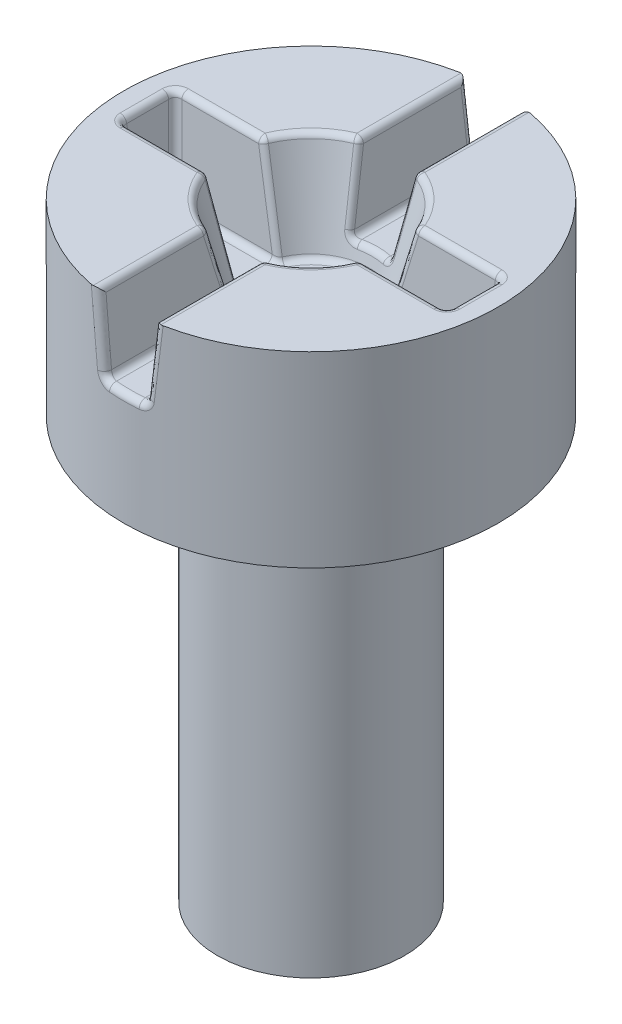
SolidWorks part; units mm, degrees
ref_plane "Front Plane" through (0, 0, 0) normal (0, 0, 1) x (1, 0, 0)
ref_plane "Top Plane" through (0, 0, 0) normal (0, 1, 0) x (1, 0, 0)
ref_plane "Right Plane" through (0, 0, 0) normal (1, 0, 0) x (0, 0, -1)
sketch "Sketch1" plane through (0, 0, 0) normal (0, 1, 0) x (1, 0, 0)
  circle A0 centre (0, 0) radius 1
  dimension "D1" = 2
extrude "Boss-Extrude1" add sketch "Sketch1" against normal blind 4.5
sketch "Sketch2" plane through (0, 0, 0) normal (0, 1, 0) x (1, 0, 0)
  circle A0 centre (0, 0) radius 2
  dimension "D1" = 4
extrude "Boss-Extrude2" add sketch "Sketch2" along normal blind 2
sketch "Sketch3" plane through (0, 2, 0) normal (0, 1, 0) x (1, 0, 0)
  line L1 (-1.75, 0.3) -> (1.75, 0.3)
  line L2 (-1.75, 0.3) -> (-1.75, -0.3)
  line L3 (-1.75, -0.3) -> (1.75, -0.3)
  line L4 (1.75, 0.3) -> (1.75, -0.3)
  line L5 (-1.75, 0.3) -> (1.75, -0.3) construction
  line L6 (-1.75, -0.3) -> (1.75, 0.3) construction
  point P0 (0, 0)
  dimension "D1" = 0.6
  dimension "D2" = 3.5
extrude "Cut-Extrude1" cut sketch "Sketch3" against normal blind 1 draft 5
sketch "Sketch4" plane through (0, 2, 0) normal (0, 1, 0) x (1, 0, 0)
  line L0 (1.75, -0.3) -> (1.75, 0.3) construction
  line L1 (-0.3, 2.5) -> (0.3, 2.5)
  line L2 (-0.3, 2.5) -> (-0.3, -2.5)
  line L3 (-0.3, -2.5) -> (0.3, -2.5)
  line L4 (0.3, 2.5) -> (0.3, -2.5)
  line L5 (-0.3, 2.5) -> (0.3, -2.5) construction
  line L6 (-0.3, -2.5) -> (0.3, 2.5) construction
  point P0 (0, 0)
  dimension "D1" = 5
extrude "Cut-Extrude2" cut sketch "Sketch4" against normal blind 0.8 draft 6
sketch "Sketch5" plane through (0, 2, 0) normal (0, 1, 0) x (1, 0, 0)
  circle A0 centre (0, 0) radius 0.875
  dimension "D1" = 1.75
extrude "Cut-Extrude3" cut sketch "Sketch5" against normal up to surface (1 mm away) draft 15
fillet "Fillet1" radius 0.07 43 edges at (-1.75, 2, 0) (-1.7063, 1.5, 0.2563) (-1.1156, 1, 0.2125) (-1.286, 2, 0.3) (-0.6187, 2, 0.6187) (-1.7063, 1.5, -0.2563) (-1.286, 2, -0.3) (-1.1156, 1, -0.2125) (0.258, 1.6006, -1.9833) (0.258, 1.6006, 1.9833) (0.2159, 1.2, -1.3063) (0.2159, 1.2, 1.3063) (0.3, 2, -1.3997) (0.3, 2, 1.3997) (0.6187, 2, 0.6187) (1.286, 2, 0.3) (1.1156, 1, 0.2125) (1.7063, 1.5, 0.2563) (1.6625, 1, 0) (1.75, 2, 0) (1.7063, 1.5, -0.2563) (1.1156, 1, -0.2125) (1.286, 2, -0.3) (-0.258, 1.6006, 1.9833) (-0.258, 1.6006, -1.9833) (-0.3, 2, 1.3997) (-0.3, 2, -1.3997) (-0.2159, 1.2, 1.3063) (-0.2159, 1.2, -1.3063) (0.6187, 2, -0.6187) (-0.6187, 2, -0.6187) (0, 1.2, -2) (0, 1.2, 2) (0, 1.2, 0.6606) (0, 1.2, -0.6606)
